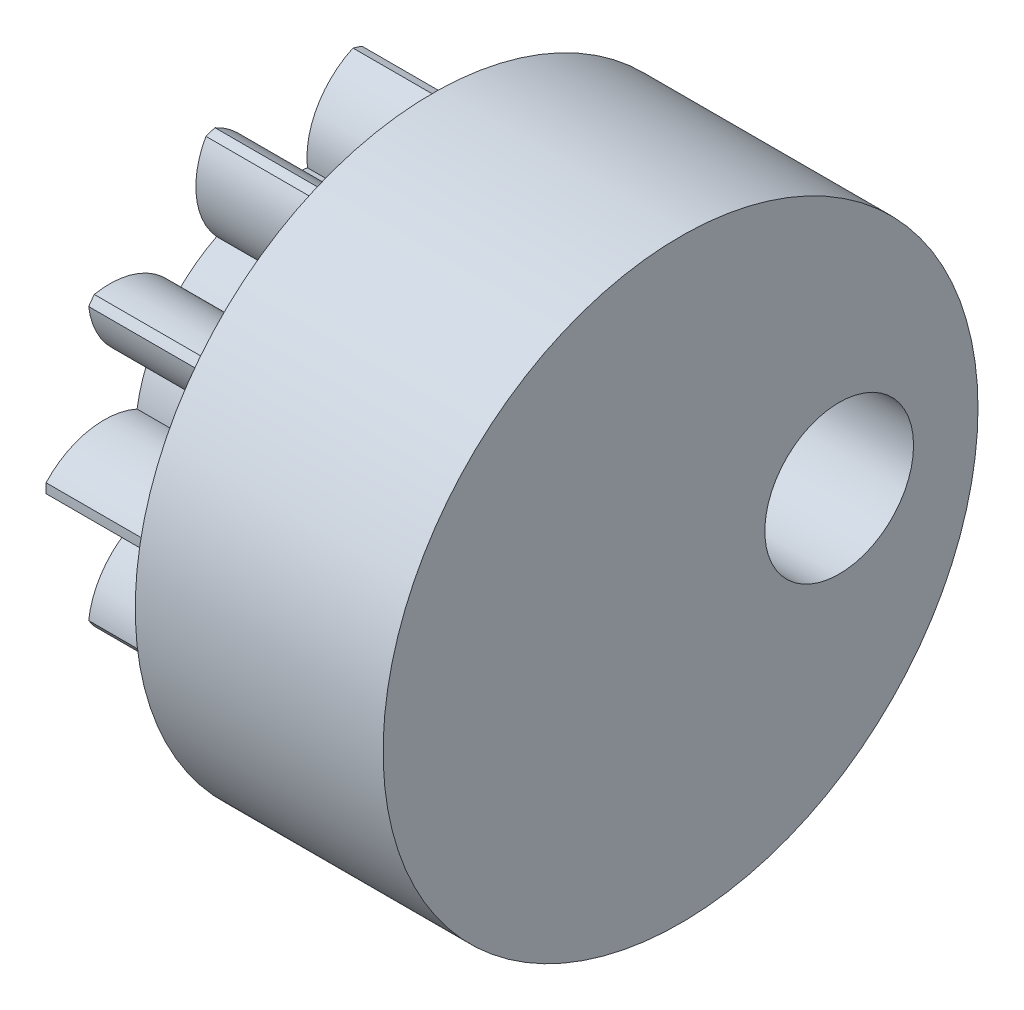
SolidWorks part; units mm, degrees
ref_plane "Plane1" through (0, 0, 0) normal (0, 0, 1) x (1, 0, 0)
ref_plane "Plane2" through (0, 0, 0) normal (0, 1, 0) x (1, 0, 0)
ref_plane "Plane3" through (0, 0, 0) normal (1, 0, 0) x (0, 0, -1)
other "Configuration Table"
sketch "HoldingSke" plane through (0, 0, 0) normal (0, 1, 0) x (1, 0, 0)
  line L0 (0, 0) -> (1.231, -0.2171)
  line L1 (-15, 0) -> (100, 0) construction
  line L2 (0, 0) -> (-2.1039, 2.3779)
  line L3 (0, 0) -> (-11.863, 4.5341)
  line L4 (0, 0) -> (8.5048, 1.4996)
  line L5 (0, 0) -> (-16.8652, -6.2902)
  line L6 (0, 0) -> (-6.6317, -4.4744)
  line L7 (-2.1039, 2.3779) -> (1.7706, 19.956)
  line L8 (-76.2, 54.61) -> (-76.1, 54.61)
  line L9 (-71.009, 38.7566) -> (-53.1078, 45.2721)
  line L10 (-76.2, 71.12) -> (104.1128, 71.12)
  line L11 (0, 0) -> (-8, 0)
  line L12 (-76.2, 101.6) -> (-76.17, 101.6)
  line L13 (24.9733, 27.94) -> (52.9518, 28.4284)
  line L14 (24.9733, 27.94) -> (24.9743, 27.94)
  line L15 (24.9733, 27.94) -> (100.4006, 29.5858)
  line L16 (-63.627, -0.8) -> (-12.827, -0.8)
  circle A0 centre (0, 0) radius 0.4
  circle A1 centre (0, 0) radius 1.9
  circle A2 centre (0, 0) radius 1.9
  circle A3 centre (0, 0) radius 0.4
  dimension "MHD" = 3.8
  dimension "Hub_dia" = 3.8
  dimension "Bore" = 0.8
  dimension "MBD" = 0.8
  dimension "Num_teeth" = 10
  dimension "Pitch" = 1.25
  dimension "Overall_len" = 18
  dimension "Show_teeth" = 10
  dimension "Thickness" = 8
  dimension "OAL" = 18.0001
  dimension "T_dim" = 0.1
  dimension "Ap" = 20
  dimension "H" = 19.05
  dimension "Pitch_radius" = 180.3128
  dimension "Width" = 8
  dimension "Backlash" = 0.03
  dimension "Addendum_fac" = 1
  dimension "Dedendum_fac" = 1.25
  dimension "Clearance_fac" = 0.25
  dimension "Dedendum_add" = 0.001
  dimension "Module" = 0.8
sketch "BasProSke" plane through (0, 0, 0) normal (0, 1, 0) x (1, 0, 0)
  line L0 (-10, 0) -> (60, 0) construction
  line L1 (0, 0) -> (0, 4.8)
  line L2 (0, 0) -> (8, 0)
  line L3 (8, 0) -> (8, 4.8)
  line L4 (8, 4.8) -> (0, 4.8)
  dimension "Thickness" = 8
  dimension "Diameter" = 9.6
revolve "Base-Revolve" add sketch "BasProSke" angle 360 about L0
sketch "TooCutSke" plane through (0, 0, 0) normal (1, 0, 0) x (0, 0, -1)
  line L1 (0, 0) -> (0, 107) construction
  line L2 (0, 0) -> (-0.6781, 3.9421) construction
  line L3 (0, 0) -> (-2.4466, 7.5299) construction
  line L4 (-0.6781, 3.9421) -> (-1.2233, 3.765) construction
  arc A0 (0.4737, 2.9613) -> (-0.4737, 2.9613) centre (0, 0) ccw
  arc A1 (1.4269, 4.6096) -> (-1.4269, 4.6096) centre (0, 0) ccw
  circle A2 centre (0, 0) radius 4 construction
  circle A3 centre (0, 0) radius 3.7588 construction
  arc A4 (-0.4737, 2.9613) -> (-1.4269, 4.6096) centre (-2.0635, 3.1417) ccw
  arc A5 (1.4269, 4.6096) -> (0.4737, 2.9613) centre (2.0635, 3.1417) ccw
  dimension "Root_dia" = 5.998
  dimension "Overcut_dia" = 9.6508
  dimension "Pitch_dia" = 8
  dimension "Base_dia" = 7.5175
  dimension "Flank_rad" = 1.6
  dimension "Half_ang" = 18
  dimension "Half_CT" = 0.5732
extrude "ToothCut" cut sketch "TooCutSke" along normal through all
fillet "Breaks" [suppressed] radius 0.016
fillet "RootFillets" [suppressed] radius 0.201
pattern_circular "TeethCuts" count 10 over 360 about axis through (0, 0, 0) along (1, 0, 0) of "ToothCut", "RootFillets", "Breaks"
sketch "HubNeaOneSke" plane through (0, 0, 0) normal (-1, 0, 0) x (0, 0, 1)
  circle A0 centre (0, 0) radius 1.9
  dimension "Diameter" = 3.8
extrude "HubNearOne" [suppressed] add sketch "HubNeaOneSke" along normal blind 10.0001
sketch "HubNeaBotSke" plane through (0, 0, 0) normal (-1, 0, 0) x (0, 0, 1)
  circle A0 centre (0, 0) radius 1.9
  dimension "Diameter" = 3.8
extrude "HubNearBoth" [suppressed] add sketch "HubNeaBotSke" along normal blind 5
ref_plane "FarPln" through (8, 0, 0) normal (1, 0, 0) x (0, 0, -1)
sketch "HubFarSke" plane through (8, 0, 0) normal (1, 0, 0) x (0, 0, -1)
  circle A0 centre (0, 0) radius 1.9
  dimension "Diameter" = 3.8
extrude "HubFar" [suppressed] add sketch "HubFarSke" along normal blind 5
sketch "BorSke" plane through (0, 0, 0) normal (1, 0, 0) x (0, 0, -1)
  circle A0 centre (0, 0) radius 0.4
  dimension "Diameter" = 0.8
extrude "Bore" cut sketch "BorSke" along normal mid plane 36.0001
sketch "KeySke" plane through (0, 0, 0) normal (1, 0, 0) x (0, 0, -1)
  line L0 (-0.05, 0) -> (-0.05, 0.5)
  line L1 (-0.05, 0.5) -> (0.05, 0.5)
  line L2 (0.05, 0.5) -> (0.05, 0)
  line L3 (0, 0) -> (0, 34) construction
  line L4 (-0.05, 0) -> (0.05, 0)
  dimension "Offset" = 0.5
  dimension "Width" = 0.1
extrude "Keyway" [suppressed] cut sketch "KeySke" along normal mid plane 36.0001
pattern_circular "Keyway2" [suppressed] count 2 every 90 about axis through (-10, 0, 0) along (1, 0, 0)
sketch "Sketch1" plane through (8, 0, 0) normal (1, 0, 0) x (0, 0, -1)
  circle A0 centre (0, 0) radius 6
  dimension "D1" = 12
extrude "Boss-Extrude1" add sketch "Sketch1" along normal blind 5
sketch "Sketch2" plane through (0, 0, 0) normal (-1, 0, 0) x (0, 0, 1)
  arc A40 (-2.9628, 0.4646) -> (-4.799, 0.096) centre (-3.6256, -0.9917) ccw
  arc A41 (-4.799, 0.096) -> (-4.799, -0.096) centre (0, 0) ccw
  arc A42 (-4.799, -0.096) -> (-2.9628, -0.4646) centre (-3.6256, 0.9917) ccw
  arc A43 (-2.9628, -0.4646) -> (-2.67, -1.3656) centre (0, 0) ccw
  arc A44 (-2.67, -1.3656) -> (-3.9389, -2.7432) centre (-2.3503, -2.9334) ccw
  arc A45 (-3.9389, -2.7432) -> (-3.8261, -2.8984) centre (0, 0) ccw
  arc A46 (-3.8261, -2.8984) -> (-2.1239, -2.1173) centre (-3.5161, -1.3288) ccw
  arc A47 (-2.1239, -2.1173) -> (-1.3574, -2.6742) centre (0, 0) ccw
  arc A48 (-1.3574, -2.6742) -> (-1.5743, -4.5345) centre (-0.1772, -3.7546) ccw
  arc A49 (-1.5743, -4.5345) -> (-1.3917, -4.5938) centre (0, 0) ccw
  arc A50 (-1.3917, -4.5938) -> (-0.4737, -2.9613) centre (-2.0635, -3.1417) ccw
  arc A51 (-0.4737, -2.9613) -> (0.4737, -2.9613) centre (0, 0) ccw
  arc A52 (0.4737, -2.9613) -> (1.3917, -4.5938) centre (2.0635, -3.1417) ccw
  arc A53 (1.3917, -4.5938) -> (1.5743, -4.5345) centre (0, 0) ccw
  arc A54 (1.5743, -4.5345) -> (1.3574, -2.6742) centre (0.1772, -3.7546) ccw
  arc A55 (1.3574, -2.6742) -> (2.1239, -2.1173) centre (0, 0) ccw
  arc A56 (2.1239, -2.1173) -> (3.8261, -2.8984) centre (3.5161, -1.3288) ccw
  arc A57 (3.8261, -2.8984) -> (3.9389, -2.7432) centre (0, 0) ccw
  arc A58 (3.9389, -2.7432) -> (2.67, -1.3656) centre (2.3503, -2.9334) ccw
  arc A59 (2.67, -1.3656) -> (2.9628, -0.4646) centre (0, 0) ccw
  arc A60 (2.9628, -0.4646) -> (4.799, -0.096) centre (3.6256, 0.9917) ccw
  arc A61 (4.799, -0.096) -> (4.799, 0.096) centre (0, 0) ccw
  arc A62 (4.799, 0.096) -> (2.9628, 0.4646) centre (3.6256, -0.9917) ccw
  arc A63 (2.9628, 0.4646) -> (2.67, 1.3656) centre (0, 0) ccw
  arc A64 (2.67, 1.3656) -> (3.9389, 2.7432) centre (2.3503, 2.9334) ccw
  arc A65 (3.9389, 2.7432) -> (3.8261, 2.8984) centre (0, 0) ccw
  arc A66 (3.8261, 2.8984) -> (2.1239, 2.1173) centre (3.5161, 1.3288) ccw
  arc A67 (2.1239, 2.1173) -> (1.3574, 2.6742) centre (0, 0) ccw
  arc A68 (1.3574, 2.6742) -> (1.5743, 4.5345) centre (0.1772, 3.7546) ccw
  arc A69 (1.5743, 4.5345) -> (1.3917, 4.5938) centre (0, 0) ccw
  arc A70 (1.3917, 4.5938) -> (0.4737, 2.9613) centre (2.0635, 3.1417) ccw
  arc A71 (0.4737, 2.9613) -> (-0.4737, 2.9613) centre (0, 0) ccw
  arc A72 (-0.4737, 2.9613) -> (-1.3917, 4.5938) centre (-2.0635, 3.1417) ccw
  arc A73 (-1.3917, 4.5938) -> (-1.5743, 4.5345) centre (0, 0) ccw
  arc A74 (-1.5743, 4.5345) -> (-1.3574, 2.6742) centre (-0.1772, 3.7546) ccw
  arc A75 (-1.3574, 2.6742) -> (-2.1239, 2.1173) centre (0, 0) ccw
  arc A76 (-2.1239, 2.1173) -> (-3.8261, 2.8984) centre (-3.5161, 1.3288) ccw
  arc A77 (-3.8261, 2.8984) -> (-3.9389, 2.7432) centre (0, 0) ccw
  arc A78 (-3.9389, 2.7432) -> (-2.67, 1.3656) centre (-2.3503, 2.9334) ccw
  arc A79 (-2.67, 1.3656) -> (-2.9628, 0.4646) centre (0, 0) ccw
  arc A80 (-2.9628, 0.4646) -> (-4.799, 0.096) centre (-3.6256, -0.9917) ccw
  arc A81 (-4.799, 0.096) -> (-4.799, -0.096) centre (0, 0) ccw
  arc A82 (-4.799, -0.096) -> (-2.9628, -0.4646) centre (-3.6256, 0.9917) ccw
  arc A83 (-2.9628, -0.4646) -> (-2.67, -1.3656) centre (0, 0) ccw
  arc A84 (-2.67, -1.3656) -> (-3.9389, -2.7432) centre (-2.3503, -2.9334) ccw
  arc A85 (-3.9389, -2.7432) -> (-3.8261, -2.8984) centre (0, 0) ccw
  arc A86 (-3.8261, -2.8984) -> (-2.1239, -2.1173) centre (-3.5161, -1.3288) ccw
  arc A87 (-2.1239, -2.1173) -> (-1.3574, -2.6742) centre (0, 0) ccw
  arc A88 (-1.3574, -2.6742) -> (-1.5743, -4.5345) centre (-0.1772, -3.7546) ccw
  arc A89 (-1.5743, -4.5345) -> (-1.3917, -4.5938) centre (0, 0) ccw
  arc A90 (-1.3917, -4.5938) -> (-0.4737, -2.9613) centre (-2.0635, -3.1417) ccw
  arc A91 (-0.4737, -2.9613) -> (0.4737, -2.9613) centre (0, 0) ccw
  arc A92 (0.4737, -2.9613) -> (1.3917, -4.5938) centre (2.0635, -3.1417) ccw
  arc A93 (1.3917, -4.5938) -> (1.5743, -4.5345) centre (0, 0) ccw
  arc A94 (1.5743, -4.5345) -> (1.3574, -2.6742) centre (0.1772, -3.7546) ccw
  arc A95 (1.3574, -2.6742) -> (2.1239, -2.1173) centre (0, 0) ccw
  arc A96 (2.1239, -2.1173) -> (3.8261, -2.8984) centre (3.5161, -1.3288) ccw
  arc A97 (3.8261, -2.8984) -> (3.9389, -2.7432) centre (0, 0) ccw
  arc A98 (3.9389, -2.7432) -> (2.67, -1.3656) centre (2.3503, -2.9334) ccw
  arc A99 (2.67, -1.3656) -> (2.9628, -0.4646) centre (0, 0) ccw
  arc A100 (2.9628, -0.4646) -> (4.799, -0.096) centre (3.6256, 0.9917) ccw
  arc A101 (4.799, -0.096) -> (4.799, 0.096) centre (0, 0) ccw
  arc A102 (4.799, 0.096) -> (2.9628, 0.4646) centre (3.6256, -0.9917) ccw
  arc A103 (2.9628, 0.4646) -> (2.67, 1.3656) centre (0, 0) ccw
  arc A104 (2.67, 1.3656) -> (3.9389, 2.7432) centre (2.3503, 2.9334) ccw
  arc A105 (3.9389, 2.7432) -> (3.8261, 2.8984) centre (0, 0) ccw
  arc A106 (3.8261, 2.8984) -> (2.1239, 2.1173) centre (3.5161, 1.3288) ccw
  arc A107 (2.1239, 2.1173) -> (1.3574, 2.6742) centre (0, 0) ccw
  arc A108 (1.3574, 2.6742) -> (1.5743, 4.5345) centre (0.1772, 3.7546) ccw
  arc A109 (1.5743, 4.5345) -> (1.3917, 4.5938) centre (0, 0) ccw
  arc A110 (1.3917, 4.5938) -> (0.4737, 2.9613) centre (2.0635, 3.1417) ccw
  arc A111 (0.4737, 2.9613) -> (-0.4737, 2.9613) centre (0, 0) ccw
  arc A112 (-0.4737, 2.9613) -> (-1.3917, 4.5938) centre (-2.0635, 3.1417) ccw
  arc A113 (-1.3917, 4.5938) -> (-1.5743, 4.5345) centre (0, 0) ccw
  arc A114 (-1.5743, 4.5345) -> (-1.3574, 2.6742) centre (-0.1772, 3.7546) ccw
  arc A115 (-1.3574, 2.6742) -> (-2.1239, 2.1173) centre (0, 0) ccw
  arc A116 (-2.1239, 2.1173) -> (-3.8261, 2.8984) centre (-3.5161, 1.3288) ccw
  arc A117 (-3.8261, 2.8984) -> (-3.9389, 2.7432) centre (0, 0) ccw
  arc A118 (-3.9389, 2.7432) -> (-2.67, 1.3656) centre (-2.3503, 2.9334) ccw
  arc A119 (-2.67, 1.3656) -> (-2.9628, 0.4646) centre (0, 0) ccw
  dimension "D1" = 0
extrude "Cut-Extrude1" cut sketch "Sketch2" against normal blind 5
sketch "Sketch4" plane through (5, 0, 0) normal (-1, 0, 0) x (0, 0, 1)
  circle A0 centre (0, 0) radius 1.5
  dimension "D1" = 3
extrude "Cut-Extrude2" cut sketch "Sketch4" against normal blind 7
sketch "Sketch8" plane through (13, 0, 0) normal (1, 0, 0) x (0, 0, -1)
  circle A0 centre (3.2, 0) radius 1.5
  circle A1 centre (0, 0) radius 1.5 construction
  circle A2 centre (0, 0) radius 1.5 construction
  dimension "D1" = 3.2
  dimension "D2" = 3
extrude "Cut-Extrude8" cut sketch "Sketch8" against normal blind 4 contours A0
equation "' \"Module@HoldingSke\" = 6.35"
equation "' \"Num_teeth@HoldingSke\" = 12"
equation "' \"Ap@HoldingSke\" =  20"
equation "' \"Ap@HoldingSke\" = 20"
equation "' \"Width@HoldingSke\" = 0.5 * 25.4"
equation "' \"Hub_dia@HoldingSke\"= 1 * 25.4"
equation "' \"Hub_dia@HoldingSke\" = 1 * 25.4"
equation "' \"Overall_len@HoldingSke\" = 1.0 * 25.4"
equation "' \"Bore@HoldingSke\" = 0.75 * 25.4"
equation "' \"T_dim@HoldingSke\" = 0.1 * 25.4"
equation "' \"Width@KeySke\" = 0.25 * 25.4"
equation "' \"Show_teeth@HoldingSke\" = 13"
equation "' \"Backlash@HoldingSke\" = 0.009 * 25.4"
equation "' \"Addendum_fac@HoldingSke\" = 1.0"
equation "' \"Dedendum_fac@HoldingSke\" = 1.25"
equation "' \"Dedendum_add@HoldingSke\" = 0.00005 * 25.4"
equation "' \"Clearance_fac@HoldingSke\" = 0.25"
equation "\"Pitch@HoldingSke\" = 1 / \"Module@HoldingSke\""
equation "\"Overcut_dia@TooCutSke\" = (\"Num_teeth@HoldingSke\" + 2 * \"Addendum_fac@HoldingSke\") / \"Pitch@HoldingSke\" + 0.002 * 25.4"
equation "\"Pitch_dia@TooCutSke\" = \"Num_teeth@HoldingSke\" / \"Pitch@HoldingSke\""
equation "\"Base_dia@TooCutSke\" = \"Num_teeth@HoldingSke\" / \"Pitch@HoldingSke\" * cos((\"Ap@HoldingSke\"  * 3.14159265 / 180))"
equation "\"Root_dia@TooCutSke\" = (\"Num_teeth@HoldingSke\" + 2) / \"Pitch@HoldingSke\" - 2 * (\"Addendum_fac@HoldingSke\" + \"Dedendum_fac@HoldingSke\") / \"Pitch@HoldingSke\" - \"Dedendum_add@HoldingSke\" * 2"
equation "\"Half_ang@TooCutSke\" = 180 / \"Num_teeth@HoldingSke\""
equation "\"Half_CT@TooCutSke\" = \"Num_teeth@HoldingSke\" / \"Pitch@HoldingSke\" * sin((3.14159265 / 2 / \"Num_teeth@HoldingSke\")) / 2 - 7 * \"Backlash@HoldingSke\" / 4"
equation "\"Flank_rad@TooCutSke\" = \"Num_teeth@HoldingSke\" / \"Pitch@HoldingSke\" / 5"
equation "\"Radius@RootFillets\" = \"Clearance_fac@HoldingSke\" / \"Pitch@HoldingSke\" + \"Dedendum_add@HoldingSke\""
equation "\"Break_rad@Breaks\" = 0.02 / \"Pitch@HoldingSke\""
equation "\"Thickness@HoldingSke\" = \"Width@HoldingSke\""
equation "\"OAL@HoldingSke\" = \"Thickness@HoldingSke\""
equation "\"MHD@HoldingSke\" = (\"Num_teeth@HoldingSke\" + 2) / \"Pitch@HoldingSke\" - 2 * (\"Addendum_fac@HoldingSke\" + \"Dedendum_fac@HoldingSke\")  / \"Pitch@HoldingSke\" - \"Dedendum_add@HoldingSke\" * 2"
equation "\"MBD@HoldingSke\" = (\"Num_teeth@HoldingSke\" + 2) / \"Pitch@HoldingSke\" - 2 * (\"Addendum_fac@HoldingSke\" + \"Dedendum_fac@HoldingSke\")  / \"Pitch@HoldingSke\" - \"Dedendum_add@HoldingSke\" * 2 - 0.002 * 25.4"
equation "\"MHD@HoldingSke\" = ((sgn( \"MHD@HoldingSke\" - \"Hub_dia@HoldingSke\" )-1)*( \"MHD@HoldingSke\" - \"Hub_dia@HoldingSke\" ))/-2+ \"Hub_dia@HoldingSke\""
equation "\"MBD@HoldingSke\" = ((sgn( \"MBD@HoldingSke\" - \"Bore@HoldingSke\" )-1)*( \"MBD@HoldingSke\" - \"Bore@HoldingSke\" ))/-2+ \"Bore@HoldingSke\""
equation "\"OAL@HoldingSke\" = ((sgn( \"OAL@HoldingSke\" - \"Overall_len@HoldingSke\" )+1)*( \"OAL@HoldingSke\" - \"Overall_len@HoldingSke\" ))/2 + \"Overall_len@HoldingSke\" + 0.000002 * 25.4"
equation "\"Num_teeth@TeethCuts\" = int( \"Show_teeth@HoldingSke\" ) + 1"
equation "\"Num_teeth@TeethCuts\" = ((sgn( \"Num_teeth@TeethCuts\" - \"Num_teeth@HoldingSke\" )-1)*( \"Num_teeth@TeethCuts\" - \"Num_teeth@HoldingSke\" ))/-2+ \"Num_teeth@HoldingSke\""
equation "\"Num_teeth@TeethCuts\" = ((sgn( \"Num_teeth@TeethCuts\" - 2.0)+1)*( \"Num_teeth@TeethCuts\" - 2.0))/2 +2.0"
equation "\"Angle@TeethCuts\" = 360.0 / \"Num_teeth@HoldingSke\""
equation "\"Diameter@BasProSke\" = (\"Num_teeth@HoldingSke\" + 2 * \"Addendum_fac@HoldingSke\") / \"Pitch@HoldingSke\""
equation "\"Thickness@BasProSke\"  = \"Thickness@HoldingSke\""
equation "' \"Fillet_rad@BasProSke\" =  \"Thickness@HoldingSke\" * 0.05"
equation "' \"Fillet_rad@BasProSke\" = \"Thickness@HoldingSke\" * 0.05"
equation "\"MHD@HoldingSke\" = ((sgn( \"MHD@HoldingSke\" - \"Root_dia@TooCutSke\" )-1)*( \"MHD@HoldingSke\" - \"Root_dia@TooCutSke\" ))/-2+ \"Root_dia@TooCutSke\""
equation "\"Diameter@HubNeaOneSke\" = \"MHD@HoldingSke\""
equation "\"Length@HubNearOne\" = \"OAL@HoldingSke\" - \"Thickness@BasProSke\""
equation "\"Diameter@HubNeaBotSke\" = \"MHD@HoldingSke\""
equation "\"Length@HubNearBoth\" = ( \"OAL@HoldingSke\" - \"Thickness@BasProSke\" ) / 2.0"
equation "\"Thickness@FarPln\" = \"Thickness@BasProSke\""
equation "\"Diameter@HubFarSke\" = \"MHD@HoldingSke\""
equation "\"Length@HubFar\" = ( \"OAL@HoldingSke\" - \"Thickness@BasProSke\" ) / 2.0"
equation "\"Diameter@BorSke\" = \"MBD@HoldingSke\""
equation "\"D1@Bore\" = \"OAL@HoldingSke\" * 2.0"
equation "\"D1@Keyway\" = \"OAL@HoldingSke\" * 2.0"
equation "\"Offset@KeySke\" = \"T_dim@HoldingSke\" + \"MBD@HoldingSke\" / 2.0"
